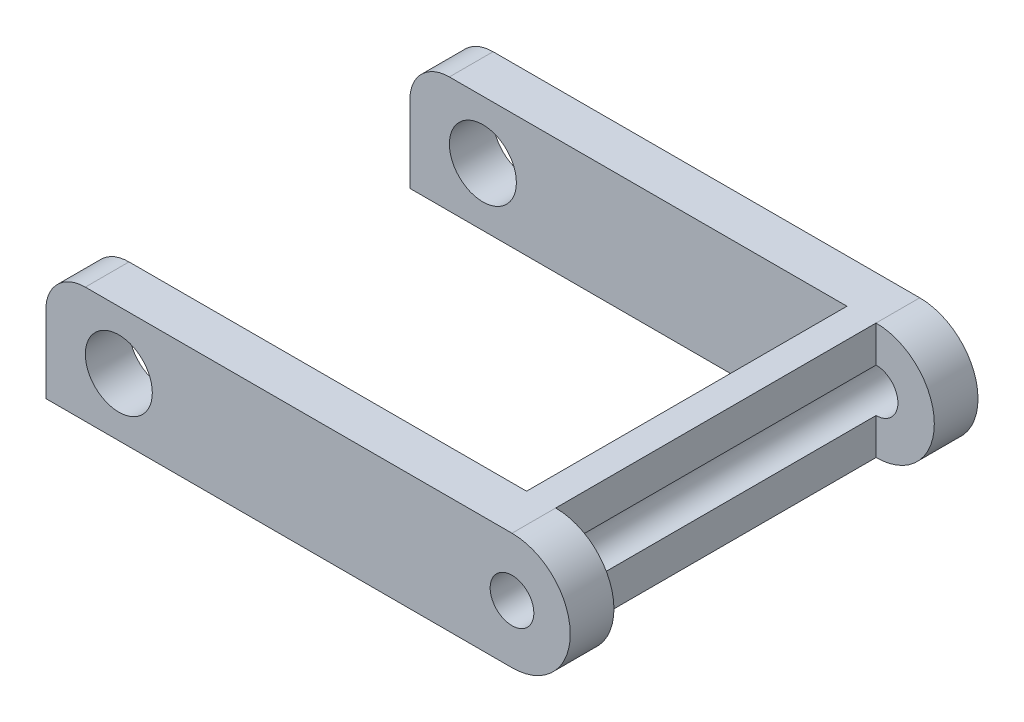
SolidWorks part; units mm, degrees
material "Nylon 6/10"
ref_plane "Front" through (0, 0, 0) normal (0, 0, 1) x (1, 0, 0)
ref_plane "Top" through (0, 0, 0) normal (0, 1, 0) x (1, 0, 0)
ref_plane "Right" through (0, 0, 0) normal (1, 0, 0) x (0, 0, -1)
sketch "Sketch1" plane through (0, 0, 0) normal (0, 0, 1) x (1, 0, 0)
sketch "Sketch2" plane through (0, 0, 0) normal (0, 0, 1) x (1, 0, 0)
  line L0 (-14.65, 1.9925) -> (0, 2)
  line L1 (-16, 0.5) -> (-16, -2)
  line L2 (-16, -2) -> (0, -2)
  arc A0 (-14.65, 1.9925) -> (-16, 0.5) centre (-14.6493, 0.6351) ccw
  arc A1 (0, -2) -> (0, 2) centre (0, 0) ccw
  circle A2 centre (-13.5, 0) radius 1.15
  circle A3 centre (0, 0) radius 0.75
sketch "Sketch3" plane through (0, 17.5397, 0) normal (0, 1, 0) x (-1, 0, 0)
  line L0 (5.5, -12.5) -> (16, -12.5)
  line L1 (16, -12.5) -> (16, -14)
  line L2 (16, -14) -> (-2, -14)
  line L3 (-2, -14) -> (-2, -12.5)
  line L4 (-2, -12.5) -> (0, -12.5)
  line L5 (0, -12.5) -> (0, -1.5)
  line L6 (0, -1.5) -> (-2, -1.5)
  line L7 (-2, -1.5) -> (-2, 0)
  line L8 (-2, 0) -> (16, 0)
  line L9 (16, 0) -> (16, -1.5)
  line L10 (16, -1.5) -> (5.5, -1.5)
  line L11 (5.5, -1.5) -> (3, -4)
  line L12 (3, -4) -> (3, -10)
  line L13 (3, -10) -> (5.5, -12.5)
  line L14 (5.5, -1.5) -> (1, -1.5)
  line L15 (1, -1.5) -> (1, -12.5)
  line L16 (1, -12.5) -> (5.5, -12.5)
sketch "Sketch4" plane through (-42.9284, 0, 0) normal (-1, 0, 0) x (0, 0, 1)
  line L0 (-10, -0.5) -> (-10, 0.5)
  line L1 (-10, 0.5) -> (-12.5, 0.5)
  line L2 (-12.5, -0.5) -> (-10, -0.5)
  line L3 (-4, -0.5) -> (-4, 0.5)
  line L4 (-1.5, 0.5) -> (-4, 0.5)
  line L5 (-4, -0.5) -> (-1.5, -0.5)
  line L6 (-4, 0.5) -> (-10, 0.5)
  line L7 (-10, -0.5) -> (-4, -0.5)
  line L8 (-12.5, 2) -> (-1.5, 2)
  line L9 (-14, 2) -> (-12.5, 2)
  line L10 (-12.5, 2) -> (-12.5, -2)
  line L11 (-12.5, -2) -> (-14, -2)
  line L12 (-14, -2) -> (-14, 2)
  line L13 (0, -2) -> (-1.5, -2)
  line L14 (-1.5, -2) -> (-1.5, 2)
  line L15 (-1.5, 2) -> (0, 2)
  line L16 (0, 2) -> (0, -2)
sketch "Sketch5" plane through (0, 0, 0) normal (0, 0, 1) x (1, 0, 0)
  line L0 (-14.65, 1.9925) -> (0, 2)
  line L1 (-16, 0.5) -> (-16, -2)
  line L2 (-16, -2) -> (0, -2)
  arc A0 (-14.65, 1.9925) -> (-16, 0.5) centre (-14.6493, 0.6351) ccw
  arc A1 (0, -2) -> (0, 2) centre (0, 0) ccw
  circle A2 centre (-13.5, 0) radius 1.15
  circle A3 centre (0, 0) radius 0.75
extrude "Base-Extrude" add sketch "Sketch5" against normal blind 14
sketch "Sketch7" plane through (0, 17.5397, 0) normal (0, 1, 0) x (-1, 0, 0)
  line L0 (5.5, -12.5) -> (16, -12.5)
  line L1 (16, -12.5) -> (16, -14)
  line L2 (16, -14) -> (-2, -14)
  line L3 (-2, -14) -> (-2, -12.5)
  line L4 (-2, -12.5) -> (0, -12.5)
  line L5 (0, -12.5) -> (0, -1.5)
  line L6 (0, -1.5) -> (-2, -1.5)
  line L7 (-2, -1.5) -> (-2, 0)
  line L8 (-2, 0) -> (16, 0)
  line L9 (16, 0) -> (16, -1.5)
  line L10 (16, -1.5) -> (5.5, -1.5)
  line L11 (5.5, -1.5) -> (1, -1.5)
  line L12 (1, -1.5) -> (1, -12.5)
  line L13 (1, -12.5) -> (5.5, -12.5)
sketch "Sketch9" plane through (0, 17.5397, 0) normal (0, 1, 0) x (-1, 0, 0)
  line L0 (5.5, -12.5) -> (16, -12.5)
  line L1 (16, -12.5) -> (16, -14)
  line L2 (16, -14) -> (-2, -14)
  line L3 (-2, -14) -> (-2, -12.5)
  line L4 (-2, -12.5) -> (0, -12.5)
  line L5 (0, -12.5) -> (0, -1.5)
  line L6 (0, -1.5) -> (-2, -1.5)
  line L7 (-2, -1.5) -> (-2, 0)
  line L8 (-2, 0) -> (16, 0)
  line L9 (16, 0) -> (16, -1.5)
  line L10 (16, -1.5) -> (5.5, -1.5)
  line L11 (5.5, -1.5) -> (1, -1.5)
  line L12 (1, -1.5) -> (1, -12.5)
  line L13 (1, -12.5) -> (5.5, -12.5)
extrude "Cut-Extrude2" cut sketch "Sketch9" against normal blind 37 flip side to cut
sketch "Sketch10" plane through (-42.9284, 0.5, -4) normal (0, 1, 0) x (-1, 0, 0)
  line L0 (-37.4284, 2.5) -> (-39.9284, 0)
  line L1 (-39.9284, 0) -> (-39.9284, -6)
  line L2 (-39.9284, -6) -> (-37.4284, -8.5)
  line L3 (-37.4284, 2.5) -> (-41.9284, 2.5)
  line L4 (-41.9284, 2.5) -> (-41.9284, -8.5)
  line L5 (-41.9284, -8.5) -> (-37.4284, -8.5)
extrude "Boss-Extrude1" [suppressed] add sketch "Sketch10" against normal blind 1
